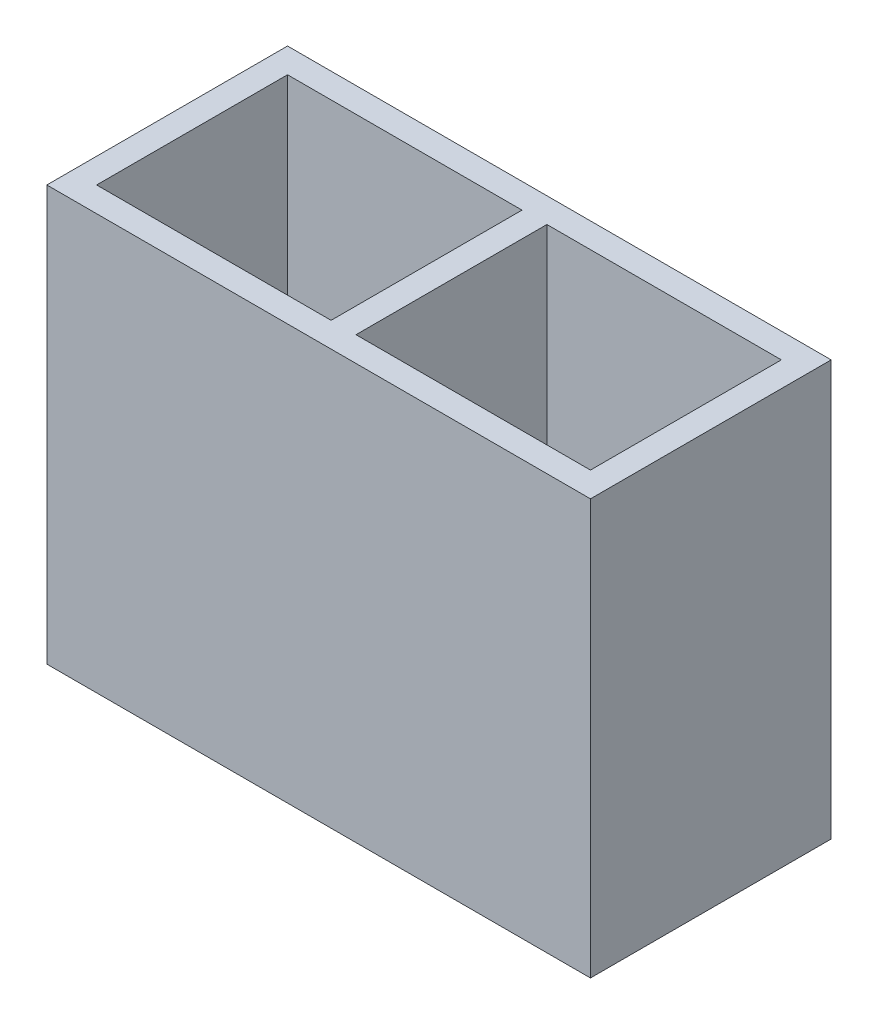
SolidWorks part; units mm, degrees
ref_plane "Plano frontal" through (0, 0, 0) normal (0, 0, 1) x (1, 0, 0)
ref_plane "Plano superior" through (0, 0, 0) normal (0, 1, 0) x (1, 0, 0)
ref_plane "Plano direito" through (0, 0, 0) normal (1, 0, 0) x (0, 0, -1)
sketch "Sketch1" plane through (0, 0, 0) normal (0, 1, 0) x (1, 0, 0)
  line L1 (-6.55, 2.9) -> (6.55, 2.9)
  line L2 (-6.55, 2.9) -> (-6.55, -2.9)
  line L3 (-6.55, -2.9) -> (6.55, -2.9)
  line L4 (6.55, 2.9) -> (6.55, -2.9)
  point P4 (0, 2.9)
  point P6 (-6.55, 0)
  dimension "D1" = 13.1
  dimension "D2" = 5.8
extrude "Boss-Extrude1" add sketch "Sketch1" along normal mid plane 10
sketch "Sketch10" plane through (0, 5, 0) normal (0, 1, 0) x (1, 0, 0)
  line L0 (6.55, 2.9) -> (-6.55, 2.9) construction
  line L1 (-5.95, 2.3) -> (-0.3, 2.3)
  line L2 (-5.95, 2.3) -> (-5.95, -2.3)
  line L3 (-5.95, -2.3) -> (-0.3, -2.3)
  line L4 (5.95, 2.3) -> (5.95, -2.3)
  line L5 (-6.55, 2.9) -> (-6.55, -2.9) construction
  line L6 (-0.3, 2.3) -> (-0.3, -2.3)
  line L7 (0, -3.19) -> (0, 3.19) construction
  line L8 (0.3, 2.3) -> (0.3, -2.3)
  line L9 (0.3, 2.3) -> (5.95, 2.3)
  line L10 (-0.3, 2.3) -> (0.3, 2.3) construction
  line L11 (0.3, -2.3) -> (5.95, -2.3)
  line L12 (-0.3, -2.3) -> (0.3, -2.3) construction
  point P6 (-5.95, 0)
  dimension "D1" = 0.6
  dimension "D2" = 0.6
  dimension "D3" = 0.6
extrude "Cut-Extrude7" cut sketch "Sketch10" against normal offset from surface (6.6 mm away) 3.4 up to face at (0, -5, 0)
sketch "Sketch9" plane through (0, 0, 0) normal (0, 1, 0) x (1, 0, 0)
  line L0 (-5.95, 2.3) -> (-0.3, 2.3) construction
  line L1 (-3.125, 2.3) -> (-3.125, -2.3) construction
  line L4 (-5.95, 2.3) -> (-0.3, 2.3) construction
  line L6 (-5.95, -2.3) -> (-5.95, 2.3) construction
  line L8 (-0.3, -2.3) -> (-5.95, -2.3) construction
  line L11 (0, -3.19) -> (0, 3.19) construction
  circle A0 centre (-4.625, 0) radius 0.75
  circle A2 centre (-1.625, 0) radius 0.75
  circle A3 centre (1.625, 0) radius 0.75
  circle A4 centre (4.625, 0) radius 0.75
  point P6 (-3.125, -2.3)
  point P12 (-3.2125, 2.3)
  point P15 (0, 0)
  point P16 (0, 0)
  point P17 (-3.125, 0)
  point P25 (-3.125, 2.3)
  dimension "D1" = 1.5
  dimension "D2" = 1.5
  dimension "D3" = 0.575
extrude "Cut-Extrude6" cut sketch "Sketch9" against normal through all both and the other way through all
